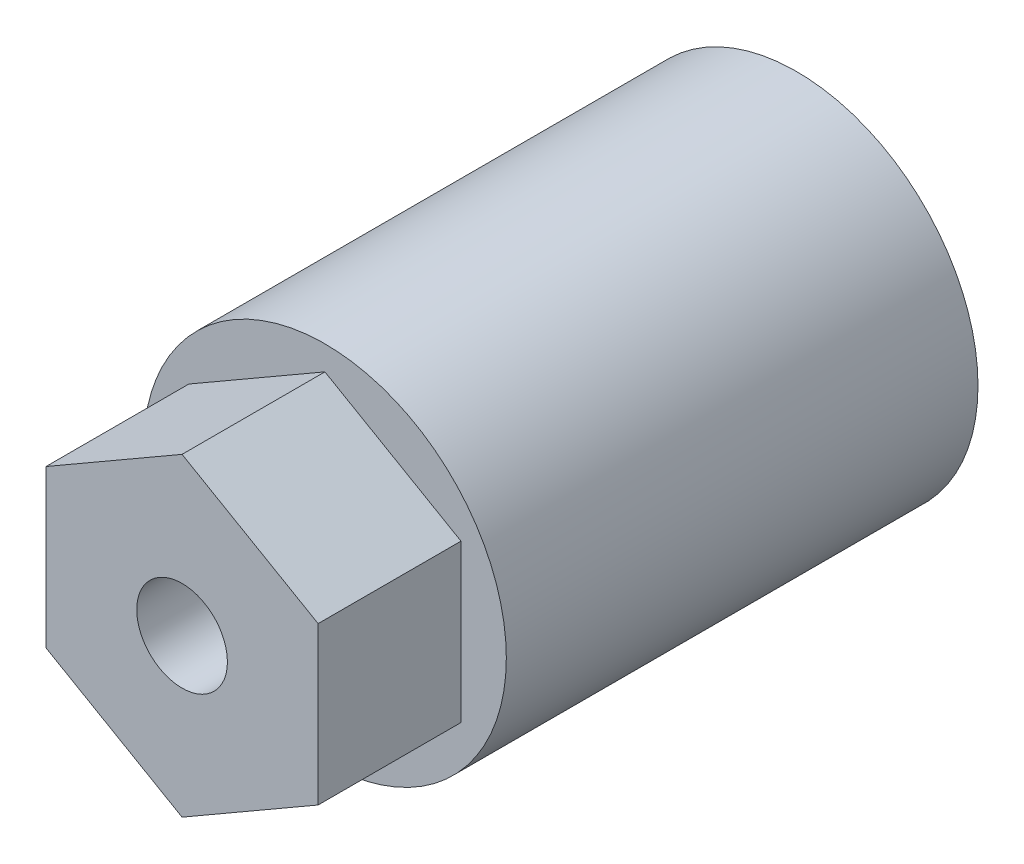
SolidWorks part; units mm, degrees
ref_plane "Alzado" through (0, 0, 0) normal (0, 0, 1) x (1, 0, 0)
ref_plane "Planta" through (0, 0, 0) normal (0, 1, 0) x (1, 0, 0)
ref_plane "Vista lateral" through (0, 0, 0) normal (1, 0, 0) x (0, 0, -1)
sketch "Croquis1" plane through (0, 0, 0) normal (0, 0, 1) x (1, 0, 0)
  circle A0 centre (0, 0) radius 8
  circle A1 centre (0, 0) radius 3.1
  dimension "D1" = 16
  dimension "D2" = 6.2
extrude "Saliente-Extruir1" add sketch "Croquis1" along normal blind 20.8
sketch "Croquis2" plane through (0, 0, 20.8) normal (0, 0, 1) x (1, 0, 0)
  circle A0 centre (0, 0) radius 3.1 construction
  circle A1 centre (0, 0) radius 8
  circle A2 centre (0, 0) radius 8 construction
  circle A3 centre (0, 0) radius 3.1
  circle A4 centre (0, 0) radius 2
  dimension "D2" = 4
  dimension "D1" = 0
extrude "Saliente-Extruir2" add sketch "Croquis2" against normal blind 2.2
sketch "Croquis3" plane through (0, 0, 20.8) normal (0, 0, 1) x (1, 0, 0)
  line L1 (0, 6.9282) -> (-6, 3.4641)
  line L2 (-6, 3.4641) -> (-6, -3.4641)
  line L3 (-6, -3.4641) -> (0, -6.9282)
  line L4 (0, -6.9282) -> (6, -3.4641)
  line L5 (6, -3.4641) -> (6, 3.4641)
  line L6 (6, 3.4641) -> (0, 6.9282)
  circle A0 centre (0, 0) radius 6 construction
  circle A1 centre (0, 0) radius 2 construction
  circle A2 centre (0, 0) radius 2
  dimension "D1" = 12
extrude "Saliente-Extruir3" add sketch "Croquis3" along normal blind 6.3
sketch "Croquis4" plane through (0, 0, 0) normal (1, 0, 0) x (0, 0, -1)
  line L0 (0, 0) -> (-6, 0) construction
  circle A0 centre (-6, 0) radius 2.5
  point P4 (-3.5, 0)
  dimension "D1" = 5
  dimension "D2" = 3.5
extrude "Cortar-Extruir1" cut sketch "Croquis4" against normal up to next
